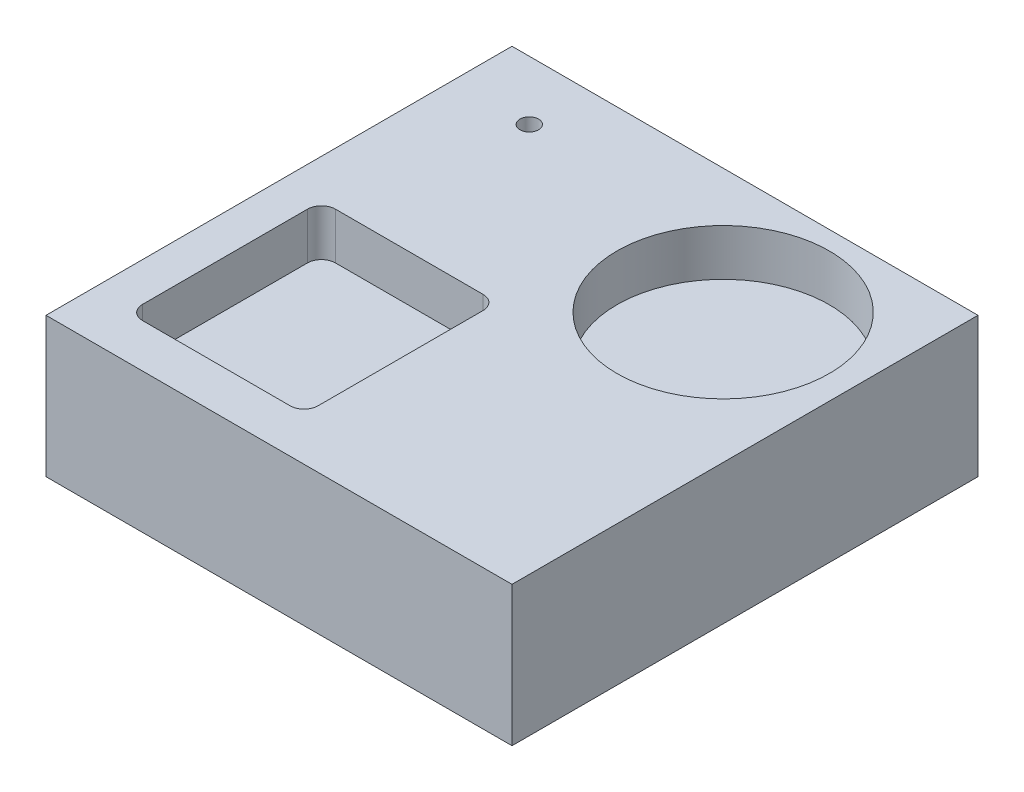
SolidWorks part; units mm, degrees
ref_plane "Front Plane" through (0, 0, 0) normal (0, 0, 1) x (1, 0, 0)
ref_plane "Top Plane" through (0, 0, 0) normal (0, 1, 0) x (1, 0, 0)
ref_plane "Right Plane" through (0, 0, 0) normal (1, 0, 0) x (0, 0, -1)
sketch "Sketch1" plane through (0, 0, 0) normal (0, 1, 0) x (1, 0, 0)
  line L1 (0, 0) -> (100, 0)
  line L2 (0, 0) -> (0, 100)
  line L3 (0, 100) -> (100, 100)
  line L4 (100, 0) -> (100, 100)
  dimension "D1" = 100
  dimension "D2" = 100
extrude "Boss-Extrude1" add sketch "Sketch1" along normal blind 30
sketch "Sketch5" plane through (0, 30, 0) normal (0, 1, 0) x (1, 0, 0)
  circle A0 centre (16.3843, 87.3232) radius 2
  dimension "D1" = 4
extrude "Cut-Extrude1" cut sketch "Sketch5" against normal through all
sketch "Sketch7" plane through (0, 30, 0) normal (0, 1, 0) x (1, 0, 0)
  line L1 (8.3279, 50.7874) -> (46.0114, 50.7874)
  line L2 (8.3279, 50.7874) -> (8.3279, 9.3741)
  line L3 (8.3279, 9.3741) -> (46.0114, 9.3741)
  line L4 (46.0114, 50.7874) -> (46.0114, 9.3741)
  circle A0 centre (72.0846, 73.2252) radius 22.79
extrude "Cut-Extrude2" cut sketch "Sketch7" against normal blind 10
fillet "Fillet1" radius 3 4 edges at (8.3279, 25, -9.3741) (46.0114, 25, -9.3741) (46.0114, 25, -50.7874) (8.3279, 25, -50.7874)
